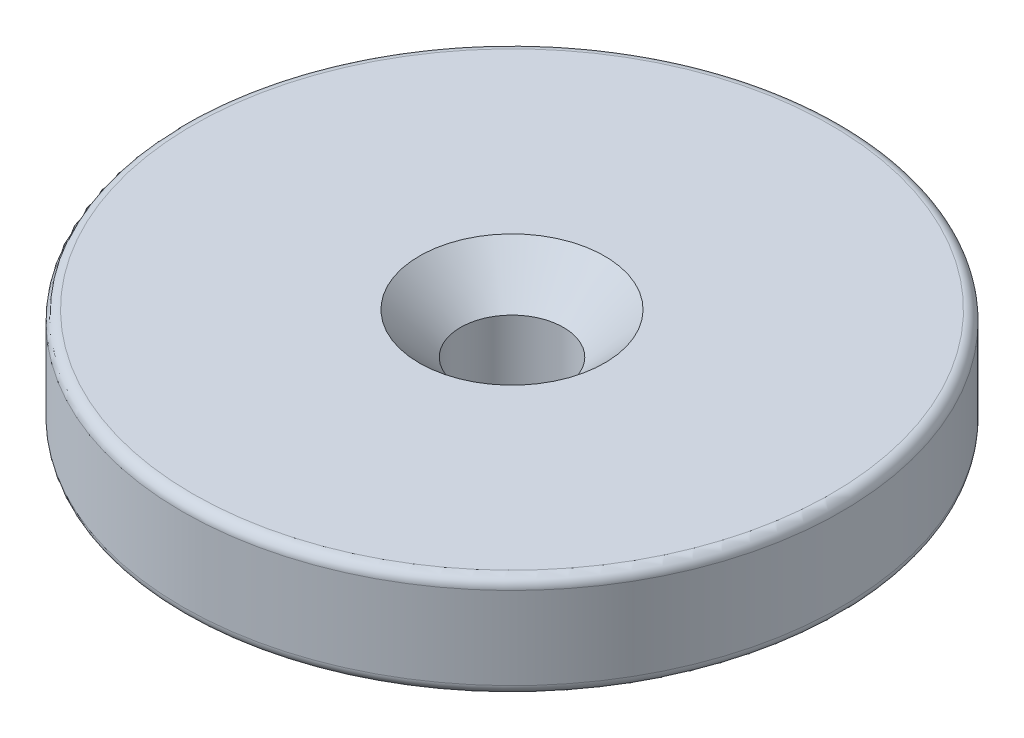
SolidWorks part; units mm, degrees
ref_plane "Front Plane" through (0, 0, 0) normal (0, 0, 1) x (1, 0, 0)
ref_plane "Top Plane" through (0, 0, 0) normal (0, 1, 0) x (1, 0, 0)
ref_plane "Right Plane" through (0, 0, 0) normal (1, 0, 0) x (0, 0, -1)
sketch "Sketch1" plane through (0, 0, 0) normal (0, 1, 0) x (1, 0, 0)
  circle A0 centre (0, 0) radius 16
  circle A1 centre (0, 0) radius 2.5
  dimension "D1" = 32
  dimension "D2" = 5
extrude "Boss-Extrude1" add sketch "Sketch1" along normal blind 5
chamfer "Chamfer1" distance 2 angle 45 1 edges at (0, 5, 2.5)
fillet "Fillet1" radius 0.5 2 edges at (0, 0, 16) (0, 5, 16)
